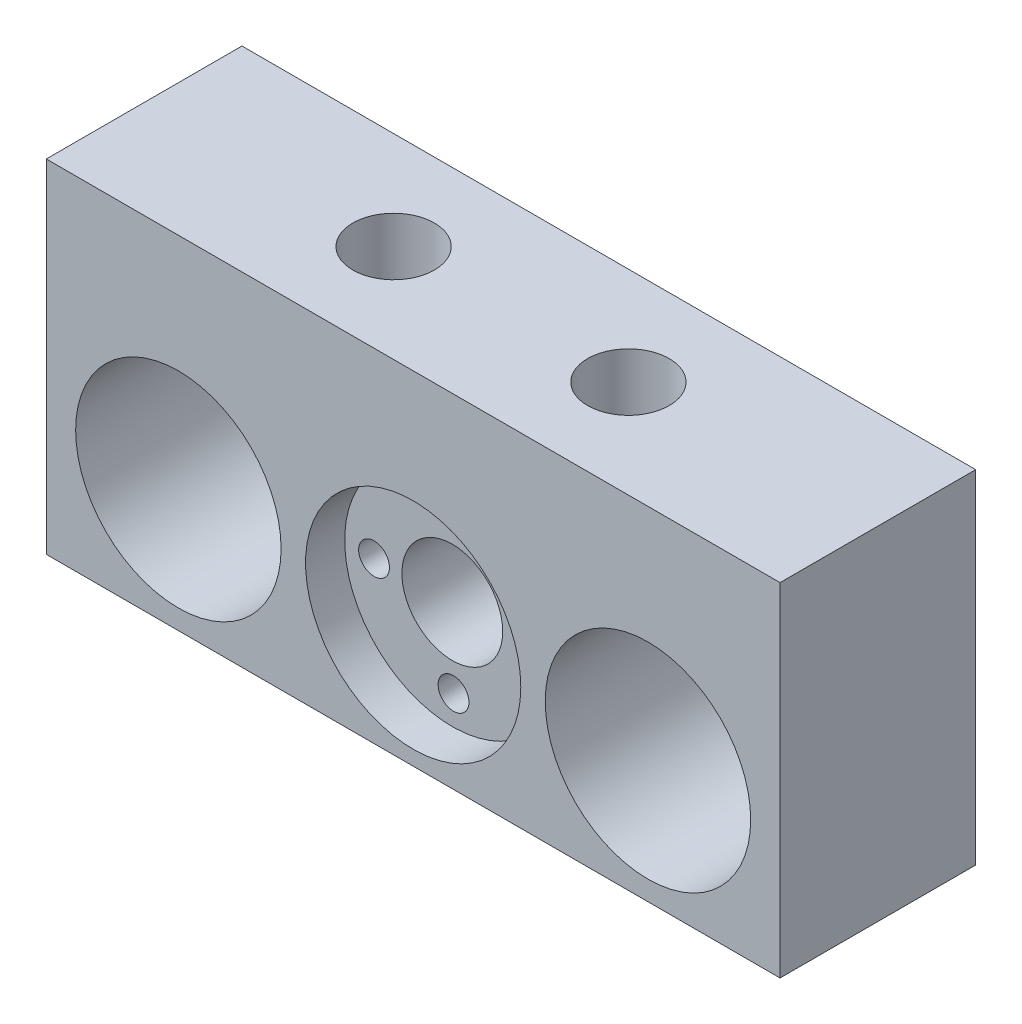
SolidWorks part; units mm, degrees
ref_plane "Plano frontal" through (0, 0, 0) normal (0, 0, 1) x (1, 0, 0)
ref_plane "Plano superior" through (0, 0, 0) normal (0, 1, 0) x (1, 0, 0)
ref_plane "Plano direito" through (0, 0, 0) normal (1, 0, 0) x (0, 0, -1)
sketch "Esboço1" plane through (0, 0, 0) normal (0, 0, 1) x (1, 0, 0)
  line L1 (37.5, -17.5) -> (-37.5, -17.5)
  line L2 (37.5, -17.5) -> (37.5, 17.5)
  line L3 (37.5, 17.5) -> (-37.5, 17.5)
  line L4 (-37.5, -17.5) -> (-37.5, 17.5)
  line L5 (37.5, -17.5) -> (-37.5, 17.5) construction
  line L6 (37.5, 17.5) -> (-37.5, -17.5) construction
  point P0 (0, 0)
  dimension "D1" = 35
  dimension "D2" = 75
extrude "Ressalto-extrusão1" add sketch "Esboço1" along normal blind 20
sketch "Esboço2" plane through (0, 0, 20) normal (0, 0, 1) x (1, 0, 0)
  line L0 (0, -16.4923) -> (0, 17.8311) construction
  line L1 (-37.5, -5) -> (37.5, -5) construction
  line L2 (-37.5, 17.5) -> (-37.5, -17.5) construction
  line L3 (37.5, -17.5) -> (37.5, 17.5) construction
  line L4 (-37.5, -17.5) -> (37.5, -17.5) construction
  circle A0 centre (-24, -5) radius 10.5
  circle A1 centre (0, -5) radius 5.15
  circle A2 centre (24, -5) radius 10.5
  dimension "D1" = 10.3
  dimension "D2" = 24
  dimension "D3" = 21
  dimension "D4" = 12.5
extrude "Corte-extrusão1" cut sketch "Esboço2" against normal through all
sketch "Esboço3" plane through (0, 0, 20) normal (0, 0, 1) x (1, 0, 0)
  line L0 (-38.7995, -5) -> (39.9542, -5) construction
  line L1 (-37.5, -17.5) -> (37.5, -17.5) construction
  circle A0 centre (0, -5) radius 11
  dimension "D1" = 22
  dimension "D2" = 12.5
extrude "Corte-extrusão2" cut sketch "Esboço3" against normal blind 4
hole_wizard "Furo roscado para conduíte de M3x0.51" positions "Esboço4" profile "Esboço5" tap size "M3x0.5" standard "Helicoil® Metric"
sketch "Esboço4" plane through (0, 0, 16) normal (0, 0, 1) x (1, 0, 0)
  line L0 (11, -5) -> (-16.7658, -5) construction
  line L2 (0, 9.047) -> (0, -20.3353) construction
  line L3 (0, -16) -> (0, 11.7658) construction
  line L4 (-11, -5) -> (16.7658, -5) construction
  line L5 (0, 6) -> (0, -21.7658) construction
  circle A0 centre (0, -5) radius 11 construction
  circle A1 centre (0, -5) radius 11 construction
  point P0 (-8, -5.1256)
  point P21 (-0.1256, 3)
  point P24 (8, -4.8744)
  point P27 (0.1256, -13)
  dimension "D1" = 8
  dimension "D2" = 4
sketch "Esboço5" plane through (-8, -5.1256, 16) normal (1, 0, 0) x (0, -1, 0)
  line L0 (0, 0) -> (0, 10.9464)
  line L1 (0, 10.9464) -> (1.575, 10)
  line L2 (1.575, 10) -> (1.575, 0)
  line L5 (1.575, 0) -> (0, 0)
  line L10 (0, 10.9464) -> (-1.575, 10) construction
  line L11 (0, -6.35) -> (0, 107.95) construction
  dimension "Tap Drill Dia." = 3.15
  dimension "Tap Drill Depth" = 10
  dimension "Drill Angle" = 118
cosmetic thread "Rosca de furo1" parameters "D1"=10, "D2"=3.716
cosmetic thread "Rosca de furo2" parameters "D1"=10, "D2"=3.716
cosmetic thread "Rosca de furo3" parameters "D1"=10, "D2"=3.716
cosmetic thread "Rosca de furo4" parameters "D1"=10, "D2"=3.716
hole_wizard "Furo roscado para conduíte de 5/16-241" positions "Esboço6" profile "Esboço7" tap size "5/16-24" standard "Helicoil® Inch"
sketch "Esboço6" plane through (0, 17.5, 0) normal (0, 1, 0) x (1, 0, 0)
  line L0 (37.5, 0) -> (-37.5, 0) construction
  line L1 (-37.5, -20) -> (-37.5, 0) construction
  line L2 (0, 11.6013) -> (0, -30.548) construction
  point P0 (-12, -10)
  point P12 (0, 0)
  point P13 (12, -10)
  dimension "D1" = 10
  dimension "D2" = 25.5
sketch "Esboço7" plane through (-12, 17.5, 10) normal (1, 0, 0) x (0, 0, 1)
  line L0 (0, 0) -> (0, 14.5037)
  line L1 (0, 14.5037) -> (4.1669, 12)
  line L2 (4.1669, 12) -> (4.1669, 0)
  line L5 (4.1669, 0) -> (0, 0)
  line L10 (0, 14.5037) -> (-4.1669, 12) construction
  line L11 (0, -6.35) -> (0, 107.95) construction
  dimension "Tap Drill Dia." = 8.3337
  dimension "Tap Drill Depth" = 12
  dimension "Drill Angle" = 118
cosmetic thread "Rosca de furo5" parameters "D1"=12, "D2"=9.398
cosmetic thread "Rosca de furo6" parameters "D1"=12, "D2"=9.398
